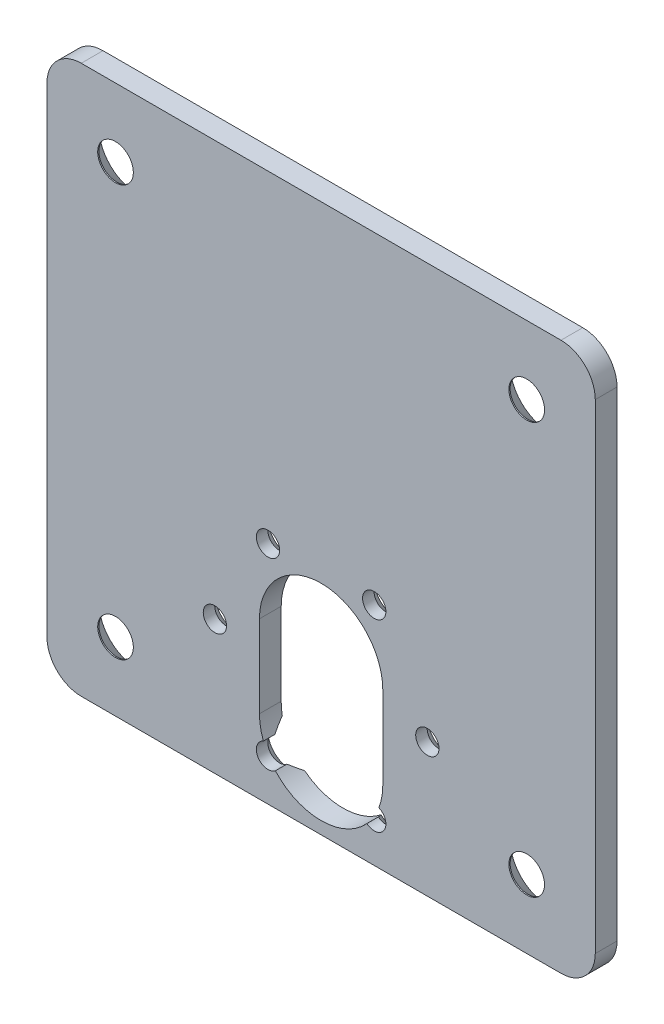
SolidWorks part; units mm, degrees
ref_plane "Front Plane" through (0, 0, 0) normal (0, 0, 1) x (1, 0, 0)
ref_plane "Top Plane" through (0, 0, 0) normal (0, 1, 0) x (1, 0, 0)
ref_plane "Right Plane" through (0, 0, 0) normal (1, 0, 0) x (0, 0, -1)
sketch "Sketch1" plane through (0, 0, 0) normal (0, 0, 1) x (1, 0, 0)
  line L0 (0, 32.9091) -> (0, -27.3797) construction
  line L1 (33.3551, 0) -> (-40.4898, 0) construction
  line L3 (35, -40) -> (-35, -40)
  line L4 (40, -35) -> (40, 35)
  line L5 (35, 40) -> (-35, 40)
  line L6 (-40, -35) -> (-40, 35)
  line L7 (40, -40) -> (-40, 40) construction
  line L8 (40, 40) -> (-40, -40) construction
  arc A0 (-40, -35) -> (-35, -40) centre (-35, -35) ccw
  arc A1 (35, -40) -> (40, -35) centre (35, -35) ccw
  arc A2 (40, 35) -> (35, 40) centre (35, 35) ccw
  arc A3 (-35, 40) -> (-40, 35) centre (-35, 35) ccw
  circle A4 centre (-30, 30) radius 2.6
  circle A5 centre (30, 30) radius 2.6
  circle A6 centre (30, -30) radius 2.6
  circle A7 centre (-30, -30) radius 2.6
  point P1 (0, 0)
  dimension "D3" = 5
  dimension "D6" = 5.2
  dimension "D1" = 80
  dimension "D2" = 80
  dimension "D4" = 10
  dimension "D5" = 10
extrude "Boss-Extrude1" add sketch "Sketch1" along normal blind 3.175
chamfer "Chamfer1" distance 3 angle 45 4 edges at (27.4, 30, 0) (-27.4, 30, 0) (32.6, -30, 0) (-32.6, -30, 0)
sketch "Sketch2" plane through (0, 0, 0) normal (0, 0, -1) x (-1, 0, 0)
  line L0 (0, 55.6275) -> (0, -91.5984) construction
  line L1 (-15.5, -20.5) -> (15.5, -20.5) construction
  line L2 (0, -20.5) -> (0, -17.8703) construction
  line L3 (0, -17.2026) -> (0, -29.2026) construction
  line L4 (35, -40) -> (-35, -40) construction
  line B0 (6.25, -10) -> (6.25, -31)
  line B1 (-6.25, -31) -> (-6.25, -10)
  circle B2 centre (-7.75, -7.0766) radius 1.5
  circle B3 centre (7.75, -7.0766) radius 1.5
  circle B4 centre (15.5, -20.5) radius 1.5
  circle B5 centre (7.75, -33.9234) radius 1.5
  circle B6 centre (-7.75, -33.9234) radius 1.5
  circle B7 centre (-15.5, -20.5) radius 1.5
  spline B8 degree 3 poles (-6.25, -10) (-6.25, -6.8332) (0, -5.1483) (6.25, -6.8333) (6.25, -10) knots 0 0 0 0 0.5 1 1 1 1
  spline B9 degree 3 poles (6.25, -31) (6.25, -33.8503) (1.8912, -34.9463) (-1.8912, -34.9463) (-6.25, -33.8501) (-6.25, -31) knots 0 0 0 0 0.45 0.55 1 1 1 1
  dimension "D1" = 19.5
sketch_block_instance "Block-Motor_Mount_reference-1"
sketch_block "Block-Motor_Mount_reference"
sketch "Sketch4" plane through (0, 0, 0) normal (0, 0, -1) x (-1, 0, 0)
  line L0 (0, -17.2026) -> (0, -29.2026) construction
  line L1 (0, 200055.6275) -> (0, -200091.5984) construction
  line L2 (9, -17.2026) -> (9, -29.2026)
  line L3 (-9, -17.2026) -> (-9, -29.2026)
  circle A2 centre (-15.5, -20.5) radius 1.7
  circle A3 centre (-15.5, -20.5) radius 1.7
  circle A5 centre (-7.75, -7.0766) radius 1.7
  circle A6 centre (-7.75, -7.0766) radius 1.7
  circle A21 centre (7.75, -7.0766) radius 1.7
  circle A22 centre (7.75, -7.0766) radius 1.7
  circle A24 centre (15.5, -20.5) radius 1.7
  circle A25 centre (15.5, -20.5) radius 1.7
  circle A27 centre (-7.75, -33.9234) radius 1.7
  arc A28 (-8.4265, -32.3638) -> (-6.6745, -35.24) centre (-7.75, -33.9234) ccw
  arc A29 (9, -17.2026) -> (-9, -17.2026) centre (0, -17.2026) ccw
  circle A30 centre (7.75, -33.9234) radius 1.7
  arc A31 (6.6745, -35.24) -> (8.4265, -32.3638) centre (7.75, -33.9234) ccw
  arc A32 (-9, -29.2026) -> (-8.4265, -32.3638) centre (0, -29.2026) ccw
  arc A33 (8.4265, -32.3638) -> (9, -29.2026) centre (0, -29.2026) ccw
  arc A34 (-6.6745, -35.24) -> (6.6745, -35.24) centre (0, -29.2026) ccw
  point P20 (0, -23.2026)
  dimension "D8" = 9
  dimension "D7" = 12
  dimension "D1" = 0.2
  dimension "D2" = 0.2
  dimension "D3" = 0.2
  dimension "D4" = 0.2
  dimension "D5" = 0.2
  dimension "D6" = 0.2
extrude "Cut-Extrude2" cut sketch "Sketch4" against normal through all
chamfer "Chamfer2" distance 1.5 angle 45 6 edges at (-9.45, -7.0766, 0) (6.05, -7.0766, 0) (9.2019, -34.8078, 0) (-9.2019, -34.8078, 0) (-17.2, -20.5, 0) (13.8, -20.5, 0)
equation "\"motor_module_height\" = 80"
equation "\"motor_module_width\" = 80"
equation "\"motor_module_length\" = 170"
equation "\"D2@Sketch1\"=\"motor_module_width\""
equation "\"D1@Sketch1\"=\"motor_module_height\""
equation "\"D5@Sketch1\"=\"D4@Sketch1\""
